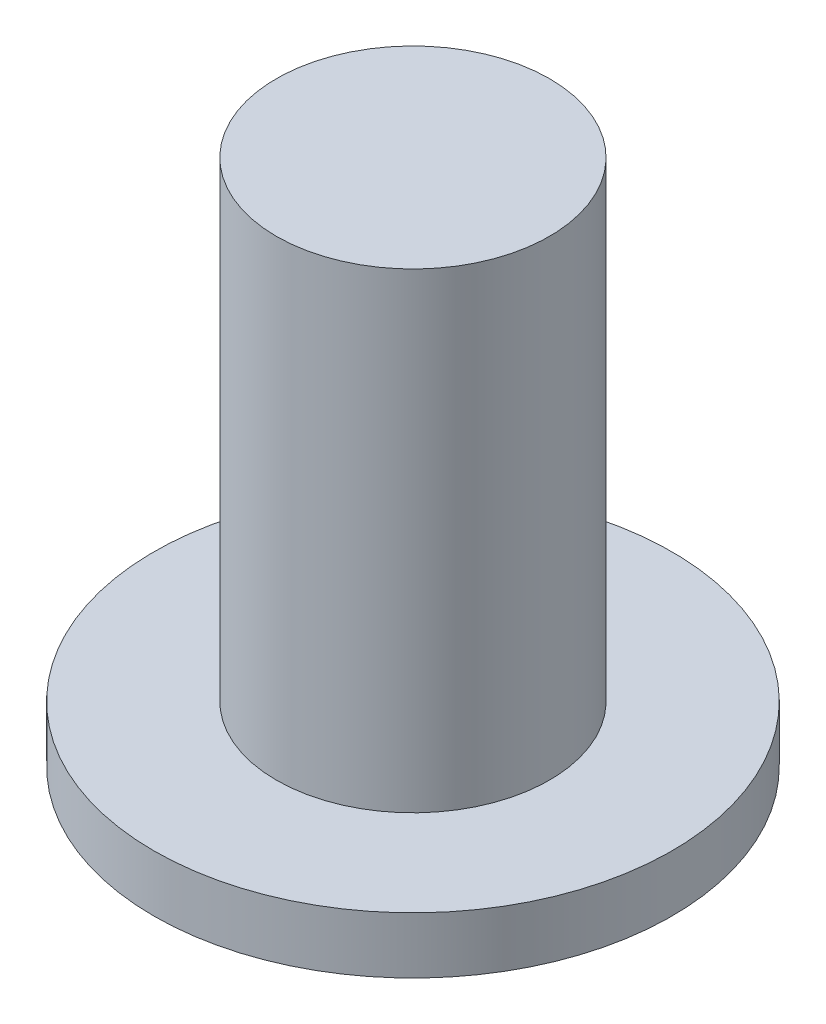
SolidWorks part; units mm, degrees
ref_plane "前视基准面" through (0, 0, 0) normal (0, 0, 1) x (1, 0, 0)
ref_plane "上视基准面" through (0, 0, 0) normal (0, 1, 0) x (1, 0, 0)
ref_plane "右视基准面" through (0, 0, 0) normal (1, 0, 0) x (0, 0, -1)
sketch "草图1" plane through (0, 0, 0) normal (0, 1, 0) x (1, 0, 0)
  circle A0 centre (0, 0) radius 2.75
  dimension "D1" = 5.5
extrude "凸台-拉伸1" add sketch "草图1" along normal blind 0.6
sketch "草图2" plane through (0, 0.6, 0) normal (0, 1, 0) x (1, 0, 0)
  circle A0 centre (0, 0) radius 1.45
  dimension "D1" = 2.9
extrude "凸台-拉伸2" add sketch "草图2" along normal blind 5
